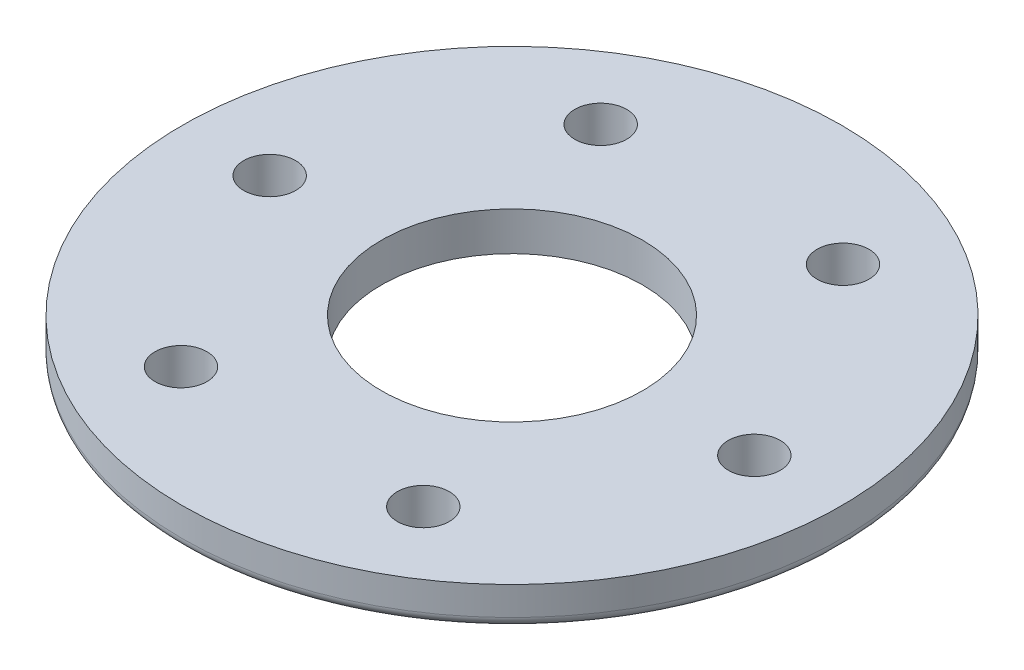
SolidWorks part; units mm, degrees
ref_plane "Front" through (0, 0, 0) normal (0, 0, 1) x (1, 0, 0)
ref_plane "Top" through (0, 0, 0) normal (0, 1, 0) x (1, 0, 0)
ref_plane "Right" through (0, 0, 0) normal (1, 0, 0) x (0, 0, -1)
ref_plane "Plane1" through (0, 0, 0) normal (0, 0, -1) x (-1, 0, 0)
sketch "Sketch1" plane through (0, 0, 0) normal (0, 0, -1) x (-1, 0, 0)
  line L0 (-32.385, 0) -> (0, 0)
  line L1 (0, 0) -> (0, 3.81)
  line L2 (0, 3.81) -> (-32.385, 3.81)
  line L3 (-32.385, 3.81) -> (-32.385, 0)
  line L4 (0, 0) -> (0, 3.81) construction
revolve "Revolve1" add sketch "Sketch1" angle 360 about L4
hole_wizard "#7 (0.201) Diameter Hole1" positions "Sketch3" profile "Sketch2" hole size "#7" standard "ANSI Inch"
sketch "Sketch3" plane through (0, 0, 0) normal (0, -1, 0) x (-1, 0, 0)
  point P0 (11.9062, 20.6222)
  point P1 (-11.9062, 20.6222)
  point P2 (-23.8125, 0)
  point P3 (-11.9062, -20.6222)
  point P4 (11.9062, -20.6222)
  point P5 (23.8125, 0)
sketch "Sketch2" plane through (-11.9062, 0, -20.6222) normal (1, 0, 0) x (0, 0, -1)
  line L0 (0, 0) -> (0, 3.81)
  line L1 (0, 3.81) -> (2.5527, 3.81)
  line L2 (2.5527, 3.81) -> (2.5527, 0)
  line L5 (2.5527, 0) -> (0, 0)
  line L11 (0, -6.35) -> (0, 107.95) construction
  dimension "Thru Hole Dia." = 5.1054
  dimension "Thru Hole Depth" = 3.81
hole_wizard "Hole1" positions "Sketch5" profile "Sketch4" legacy
sketch "Sketch5" plane through (0, 0, 0) normal (0, -1, 0) x (-1, 0, 0)
  point P0 (0, 0)
sketch "Sketch4" plane through (0, 0, 0) normal (1, 0, 0) x (0, 0, -1)
  line L0 (0, 0) -> (0, 3.81)
  line L1 (0, 3.81) -> (12.827, 3.81)
  line L2 (12.827, 3.81) -> (12.827, 0)
  line L3 (12.827, 0) -> (0, 0)
  line L4 (0, 110) -> (0, -10) construction
  dimension "Diameter" = 25.654
  dimension "Depth" = 3.81
fillet "Fillet1" radius 1 1 edges at (0, 0, 32.385)
